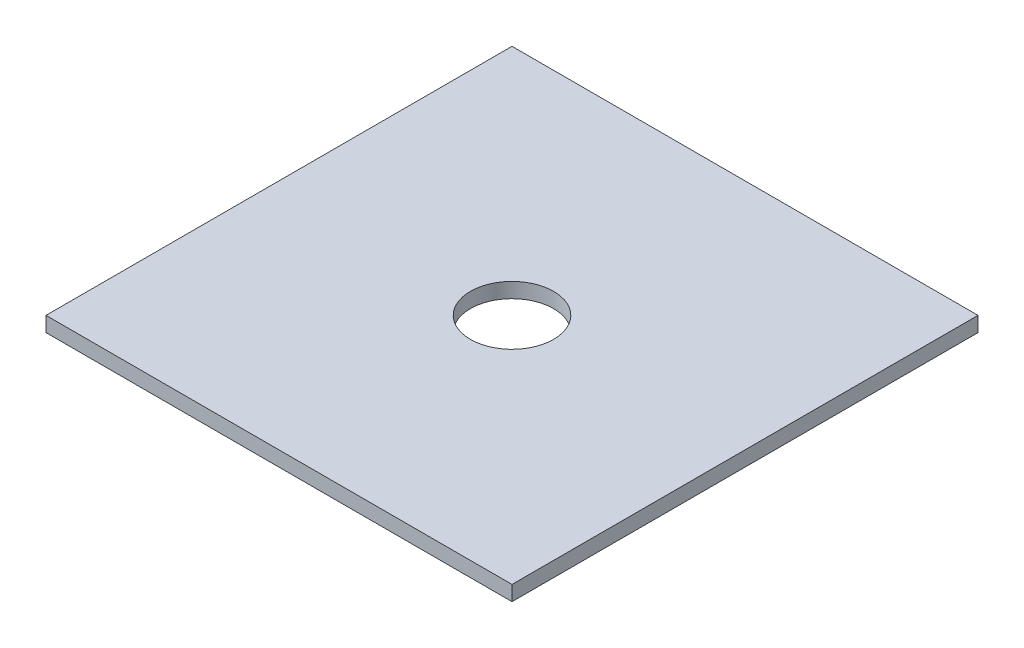
SolidWorks part; units mm, degrees
ref_plane "정면" through (0, 0, 0) normal (0, 0, 1) x (1, 0, 0)
ref_plane "윗면" through (0, 0, 0) normal (0, 1, 0) x (1, 0, 0)
ref_plane "우측면" through (0, 0, 0) normal (1, 0, 0) x (0, 0, -1)
sketch "스케치1" plane through (0, 0, 0) normal (0, 1, 0) x (1, 0, 0)
  line L1 (-280, -280) -> (280, -280)
  line L2 (-280, -280) -> (-280, 280)
  line L3 (-280, 280) -> (280, 280)
  line L4 (280, -280) -> (280, 280)
  line L5 (-280, -280) -> (280, 280) construction
  line L6 (-280, 280) -> (280, -280) construction
  point P0 (0, 0)
  dimension "D1" = 560
  dimension "D2" = 560
extrude "보스-돌출1" add sketch "스케치1" along normal blind 18
sketch "스케치2" plane through (0, 18, 0) normal (0, 1, 0) x (1, 0, 0)
  line L0 (0, 0) -> (350.4465, 0) construction
  line L1 (0, 0) -> (0, 316.6395) construction
  circle A0 centre (0, 0) radius 50
extrude "컷-돌출1" cut sketch "스케치2" against normal through all
